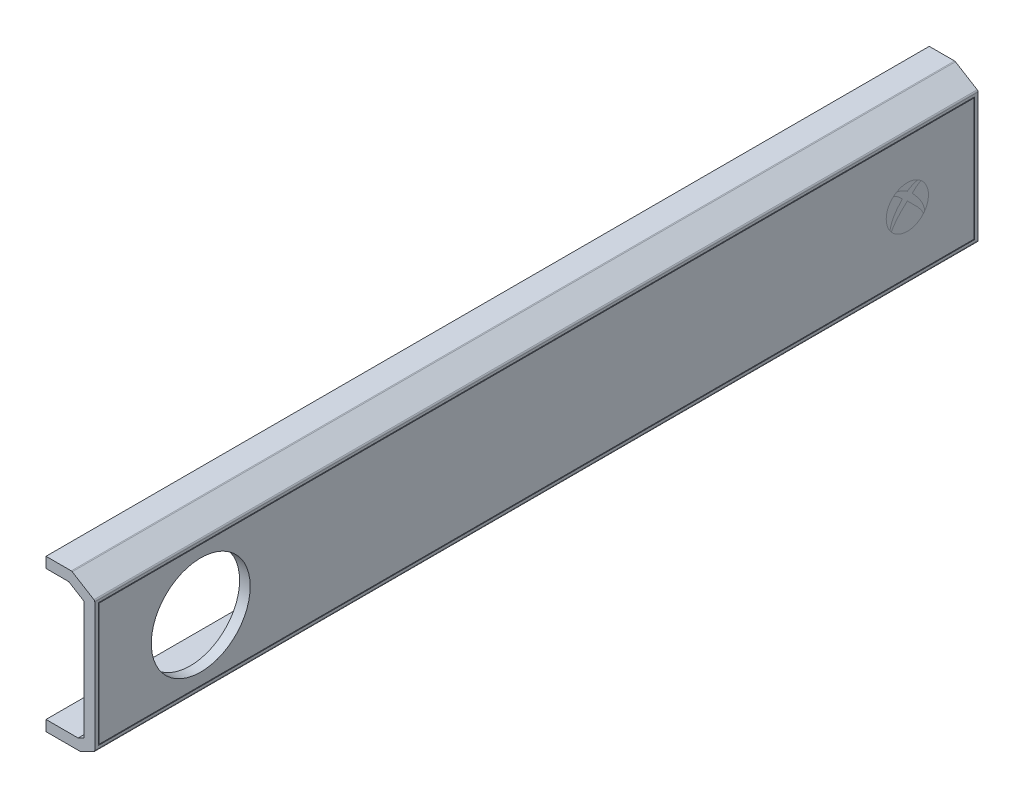
SolidWorks part; units mm, degrees
ref_plane "Front Plane" through (0, 0, 0) normal (0, 0, 1) x (1, 0, 0)
ref_plane "Top Plane" through (0, 0, 0) normal (0, 1, 0) x (1, 0, 0)
ref_plane "Right Plane" through (0, 0, 0) normal (1, 0, 0) x (0, 0, -1)
sketch "Sketch1" plane through (0, 0, 0) normal (0, 0, 1) x (1, 0, 0)
  line L0 (0, 3) -> (9.0918, 3)
  line L1 (9.0918, 3) -> (10.8, 3.8541)
  line L2 (10.8, 3.8541) -> (10.8, 37.3236)
  line L3 (10.8, 37.3236) -> (6.4509, 40)
  line L4 (6.4509, 40) -> (0, 40)
  line L5 (7.3, 43) -> (0, 43)
  line L6 (7.3, 43) -> (13.8, 39)
  line L7 (13.8, 2) -> (13.8, 39)
  line L8 (13.8, 2) -> (9.8, 0)
  line L9 (0, 0) -> (9.8, 0)
  line L10 (0, 43) -> (0, 40)
  line L11 (0, 3) -> (0, 0)
  dimension "D1" = 13.8
  dimension "D2" = 3
  dimension "D3" = 43
  dimension "D4" = 6.5
  dimension "D5" = 4
  dimension "D6" = 4
  dimension "D7" = 2
  dimension "D8" = 3
  dimension "D9" = 3
  dimension "D10" = 3
extrude "Boss-Extrude1" add sketch "Sketch1" along normal blind 250
sketch "Sketch2" plane through (0, 0, 0) normal (0, -1, 0) x (1, 0, 0)
  line L0 (13.8, 125) -> (10.8, 125) construction
  line L1 (0, 182) -> (10.8, 182)
  line L2 (0, 182) -> (0, 68)
  line L3 (0, 68) -> (10.8, 68)
  line L4 (10.8, 182) -> (10.8, 68)
  line L5 (13.8, 250) -> (13.8, 0) construction
  line L6 (0, 250) -> (0, 0) construction
  dimension "D1" = 114
  dimension "D2" = 3
extrude "Cut-Extrude1" cut sketch "Sketch2" against normal up to next
sketch "Sketch3" plane through (13.8, 0, 0) normal (1, 0, 0) x (0, 0, -1)
  line L8 (-248.8, 37.8) -> (-248.8, 3.2)
  line L9 (-248.8, 3.2) -> (-1.2, 3.2)
  line L10 (-1.2, 3.2) -> (-1.2, 37.8)
  line L11 (-1.2, 37.8) -> (-248.8, 37.8)
  line L12 (-1, 3) -> (-1, 38)
  line L13 (-1, 38) -> (-249, 38)
  line L14 (-249, 38) -> (-249, 3)
  line L15 (-249, 3) -> (-1, 3)
  line L16 (-1, 3) -> (-1, 38)
  line L17 (-1, 38) -> (-249, 38)
  line L18 (-249, 38) -> (-249, 3)
  line L19 (-249, 3) -> (-1, 3)
  dimension "D1" = 1
  dimension "D2" = 0.2
extrude "Cut-Extrude2" cut sketch "Sketch3" against normal blind 0.2
fillet "Fillet1" radius 0.5 5 edges at (9.8, 0, 34) (9.8, 0, 216) (13.8, 2, 125) (13.8, 39, 125) (7.3, 43, 125)
sketch "Sketch4" plane through (13.8, 0, 0) normal (1, 0, 0) x (0, 0, -1)
  line L0 (-220, 20.5148) -> (-250, 20.5148) construction
  line L1 (-250, 2.309) -> (-250, 38.7206) construction
  circle A0 centre (-220, 20.5148) radius 14
  dimension "D2" = 28
  dimension "D1" = 30
extrude "Cut-Extrude3" cut sketch "Sketch4" against normal through all
sketch "Sketch5" plane through (13.8, 0, 0) normal (1, 0, 0) x (0, 0, -1)
  line L0 (0, 2.309) -> (0, 38.7206) construction
  line L1 (0, 20.5148) -> (-20, 20.5148) construction
  dimension "D1" = 20
sketch_block_instance "Block1-1"
sketch_block "Block1"
split line "Split Line2"
